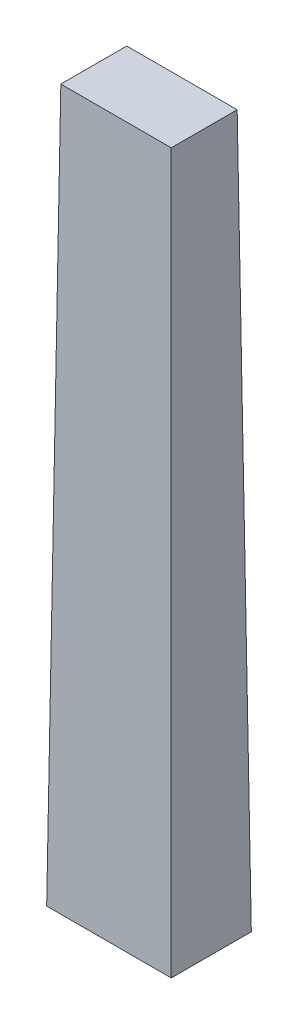
SolidWorks part; units mm, degrees
ref_plane "Front Plane" through (0, 0, 0) normal (0, 0, 1) x (1, 0, 0)
ref_plane "Top Plane" through (0, 0, 0) normal (0, 1, 0) x (1, 0, 0)
ref_plane "Right Plane" through (0, 0, 0) normal (1, 0, 0) x (0, 0, -1)
sketch "Sketch1" plane through (0, 0, 0) normal (0, 1, 0) x (1, 0, 0)
  line L2 (-8.096, 9.1839) -> (5.904, 9.1839)
  line L3 (-8.096, 9.1839) -> (-8.096, 0.1839)
  line L4 (-8.096, 0.1839) -> (5.904, 0.1839)
  line L5 (5.904, 9.1839) -> (5.904, 0.1839)
  dimension "D1" = 14
  dimension "D2" = 9
extrude "Boss-Extrude3" add sketch "Sketch1" along normal blind 80 draft 0.57
